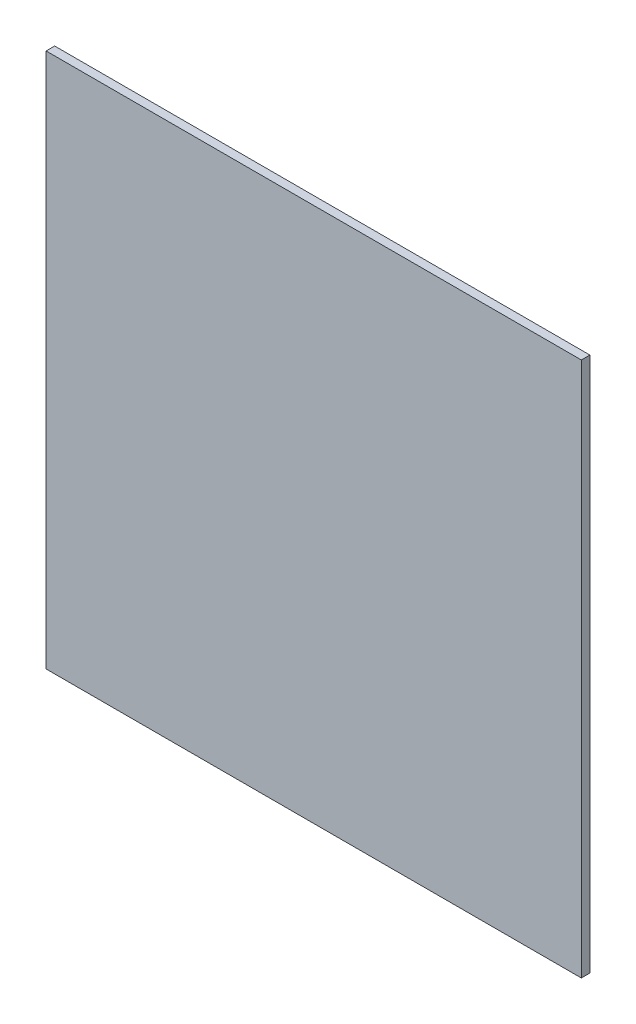
SolidWorks part; units mm, degrees
ref_plane "Plano frontal" through (0, 0, 0) normal (0, 0, 1) x (1, 0, 0)
ref_plane "Plano superior" through (0, 0, 0) normal (0, 1, 0) x (1, 0, 0)
ref_plane "Plano direito" through (0, 0, 0) normal (1, 0, 0) x (0, 0, -1)
sketch "Esboço1" plane through (0, 0, 0) normal (0, 0, 1) x (1, 0, 0)
  line L1 (-62.5, -62.5) -> (62.5, -62.5)
  line L2 (-62.5, -62.5) -> (-62.5, 62.5)
  line L3 (-62.5, 62.5) -> (62.5, 62.5)
  line L4 (62.5, -62.5) -> (62.5, 62.5)
  line L5 (-62.5, -62.5) -> (62.5, 62.5) construction
  line L6 (-62.5, 62.5) -> (62.5, -62.5) construction
  point P0 (0, 0)
  dimension "D1" = 125
  dimension "D2" = 125
extrude "Ressalto-extrusão1" add sketch "Esboço1" along normal blind 2
